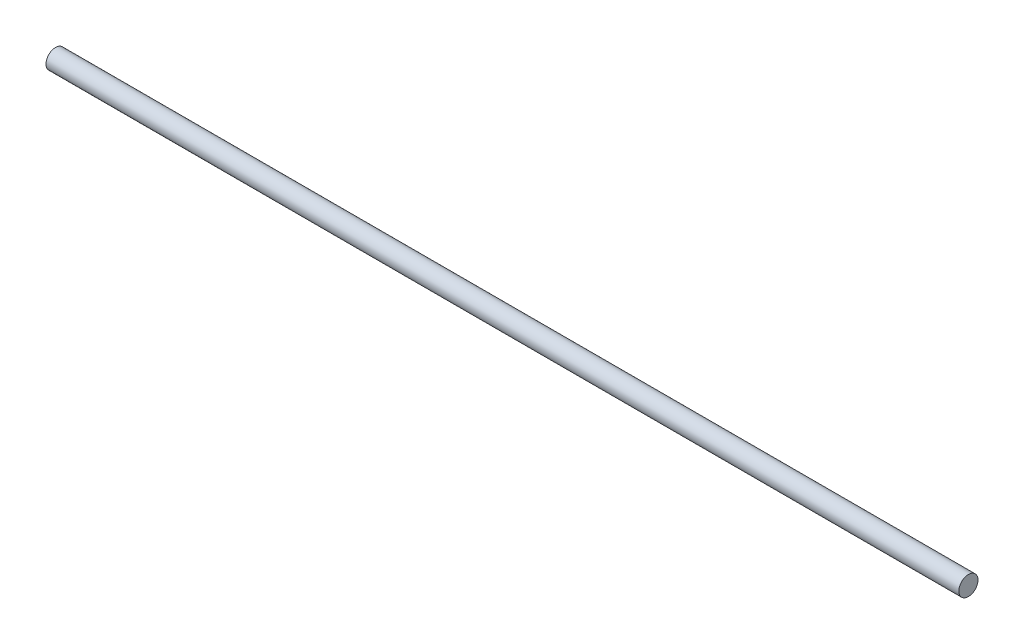
SolidWorks part; units mm, degrees
ref_plane "Front Plane" through (0, 0, 0) normal (0, 0, 1) x (1, 0, 0)
ref_plane "Top Plane" through (0, 0, 0) normal (0, 1, 0) x (1, 0, 0)
ref_plane "Right Plane" through (0, 0, 0) normal (1, 0, 0) x (0, 0, -1)
sketch "Sketch1" plane through (0, 0, 0) normal (1, 0, 0) x (0, 0, -1)
  circle A0 centre (0, 0) radius 1.5875
  dimension "D1" = 3.175
extrude "Boss-Extrude1" add sketch "Sketch1" along normal mid plane 151.13
